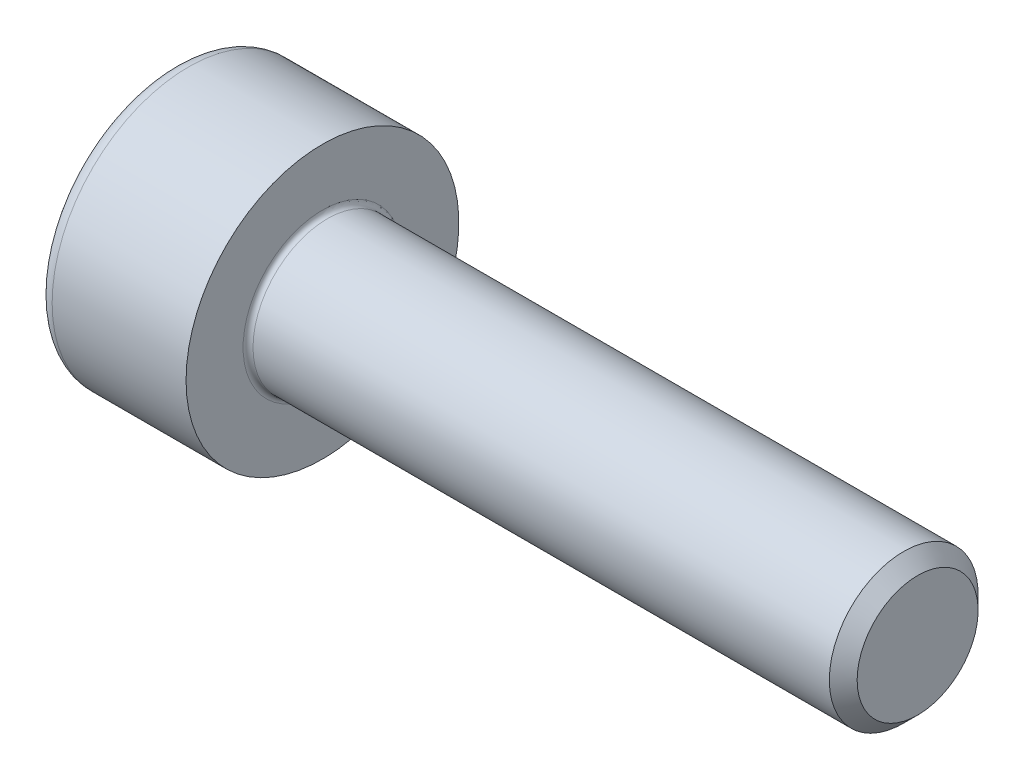
SolidWorks part; units mm, degrees
revolve "Base-Revolve" add sketch "BodySke"
sketch "BodySke" plane through (0, 0, 0) normal (0, 0, 1) x (1, 0, 0)
  line L0 (0, 0) -> (0, 2.75)
  line L1 (0, 2.75) -> (3, 2.75)
  line L2 (3, 2.75) -> (3, 1.5)
  line L3 (3, 1.5) -> (14.7195, 1.5)
  line L4 (15, 1.2195) -> (15, 0)
  line L5 (15, 0) -> (0, 0)
  line L6 (-31.75, 0) -> (127, 0) construction
  line L8 (15, 1.2195) -> (14.7195, 1.5)
  line L10 (15, -1.2195) -> (14.7195, -1.5) construction
  line L11 (3.5, 9.525) -> (3.5, 3.175) construction
  line L12 (10, 9.525) -> (10, 3.175) construction
  line L13 (-45, 9.525) -> (-45, 3.175) construction
  dimension "Head_ht" = 3
  dimension "Length" = 12
  dimension "Body_ch_ang" = 45
  dimension "Diameter" = 3
  dimension "Minor_dia" = 2.439
  dimension "Advance" = 0.5
  dimension "Thread_nom" = 5
  dimension "Thread_length" = 60
  dimension "Head_dia" = 5.5
cosmetic thread "ThreadCosmetic" [suppressed]
fillet "Fillet1" radius 0.1 1 edges at (3, 0, 1.5)
fillet "Fillet2" radius 0.3 1 edges at (0, 0, 2.75)
ref_plane "Plane1" through (0, 0, 0) normal (0, 0, 1) x (1, 0, 0)
ref_plane "Plane2" through (0, 0, 0) normal (0, 1, 0) x (1, 0, 0)
ref_plane "Plane3" through (0, 0, 0) normal (1, 0, 0) x (0, 0, -1)
other "Configuration Table"
sketch "Sketch2" plane through (0, 0, 0) normal (0, 0, 1) x (1, 0, 0)
  line L0 (0, 1.26) -> (1.3, 1.26)
  line L1 (1.3, 1.26) -> (2.0275, 0)
  line L2 (-31.75, 0) -> (127, 0) construction
  line L3 (2.0275, 0) -> (0, 0)
  line L4 (0, 0) -> (0, 1.26)
  line L6 (0, 0) -> (47.625, 0) construction
  dimension "D1" = 1.26
  dimension "D2" = 60
  dimension "Depth" = 1.3
revolve "Hex-PreBroach" cut sketch "Sketch2" angle 360 about L6
sketch "Sketch3" plane through (0, 0, 0) normal (-1, 0, 0) x (0, 0.5, 0.866)
  line L0 (0.7275, 1.26) -> (-0.7275, 1.26)
  line L1 (-0.7275, 1.26) -> (-1.4549, 0)
  line L2 (0.7275, 1.26) -> (1.4549, 0)
  line L3 (0.7275, -1.26) -> (1.4549, 0)
  line L4 (0.7275, -1.26) -> (-0.7275, -1.26)
  line L5 (-0.7275, -1.26) -> (-1.4549, 0)
  dimension "D1" = 1.26
  dimension "D2" = 1.26
  dimension "Hex_size" = 2.52
extrude "Hex" cut sketch "Sketch3" against normal blind 1.3
sketch "ThdSchSke" plane through (0, 0, 0) normal (0, 0, 1) x (1, 0, 0)
  line L0 (10, -1.2195) -> (9.8036, -1.5)
  line L1 (10, -1.2195) -> (10.1964, -1.5)
  line L2 (10.1964, -1.5) -> (10.1964, -1.875)
  line L3 (-3.175, 0) -> (5.1513, 0) construction
  line L4 (0, 2.45) -> (0, -2.45) construction
  line L5 (10.1964, -1.875) -> (9.8036, -1.875)
  line L6 (9.8036, -1.875) -> (9.8036, -1.5)
  dimension "Thread_minor" = 2.439
  dimension "Diameter" = 3
  dimension "Start" = 10
revolve "ThreadSchematic" [suppressed] cut sketch "ThdSchSke" angle 360 about L3
pattern_linear "ThdSchPat" [suppressed]
equation "\"D2@Sketch3\" = \"Hex_size@Sketch3\" / 2"
equation "\"D1@Sketch3\" = \"Hex_size@Sketch3\" / 2"
equation "\"D1@Sketch2\" = \"Hex_size@Sketch3\" / 2"
equation "\"Thread_minor@ThreadCosmetic\"  =  \"Minor_dia@BodySke\""
equation "\"Depth@Sketch2\" =  \"Key_eng@Hex\""
equation "\"Thread_length@ThreadCosmetic\" = ((sgn( (\"Length@BodySke\" - \"Advance@BodySke\" * 3.0) - \"Thread_nom@BodySke\" )-1)*( (\"Length@BodySke\" - \"Advance@BodySke\" * 3.0) - \"Thread_nom@BodySke\" ))/-2+ \"Thread_nom@BodySke\""
equation "\"Thread_minor@ThdSchSke\" = \"Minor_dia@BodySke\""
equation "\"Diameter@ThdSchSke\" = \"Diameter@BodySke\""
equation "\"Overcut@ThdSchSke\" = \"Diameter@BodySke\" * 1.25"
equation "\"Start@ThdSchSke\" = \"Head_ht@BodySke\" + \"Length@BodySke\" - \"Thread_length@ThreadCosmetic\"  '---Non-countersunk---"
equation "\"Num_threads@ThdSchPat\" = int( \"Thread_length@ThreadCosmetic\" / \"Advance@BodySke\" + 0.999 )  + 1"
equation "\"Advance@ThdSchPat\" = \"Thread_length@ThreadCosmetic\" /  (\"Num_threads@ThdSchPat\" - 1) 'relax it"
equation "\"Num_threads@ThdSchPat\" = \"Num_threads@ThdSchPat\" - sgn( \"Num_threads@ThdSchPat\" - 1) '---chamfered tips only---"
